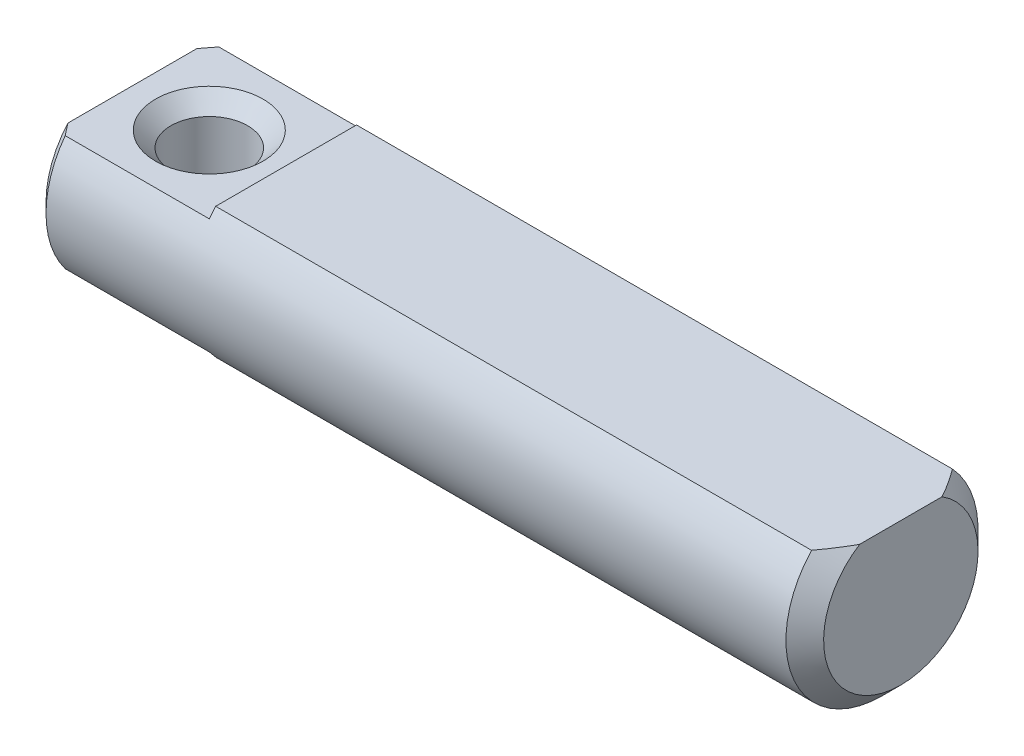
SolidWorks part; units mm, degrees
ref_plane "Front Plane" through (0, 0, 0) normal (0, 0, 1) x (1, 0, 0)
ref_plane "Top Plane" through (0, 0, 0) normal (0, 1, 0) x (1, 0, 0)
ref_plane "Right Plane" through (0, 0, 0) normal (1, 0, 0) x (0, 0, -1)
ref_plane "Plane1" through (0, 0, 0) normal (0, 0, 1) x (1, 0, 0)
sketch "Sketch1" plane through (0, 0, 0) normal (0, 0, 1) x (1, 0, 0)
  line L0 (0, 0) -> (0, 2.25)
  line L1 (0, 2.25) -> (0.25, 2.5)
  line L2 (0.25, 2.5) -> (19.5095, 2.5)
  line L3 (19.5095, 2.5) -> (20, 2.0095)
  line L4 (20, 2.0095) -> (20, 0)
  line L5 (20, 0) -> (0, 0)
  line L6 (20, 0) -> (0, 0) construction
revolve "Revolve1" add sketch "Sketch1" angle 360 about L6
cosmetic thread "Cosmetic Thread1" parameters "D1"=15, "D2"=4.11
ref_plane "Plane2" through (0, 0, 0) normal (1, 0, 0) x (0, 0, -1)
sketch "Sketch2" plane through (0, 0, 0) normal (1, 0, 0) x (0, 0, -1)
  line L0 (-10, 1.5) -> (10, 1.5)
  line L1 (10, 1.5) -> (10, 4.5)
  line L2 (10, 4.5) -> (-10, 4.5)
  line L3 (-10, 4.5) -> (-10, 1.5)
extrude "Cut-Extrude1" cut sketch "Sketch2" along normal blind 4
ref_plane "Plane3" through (0, 0, 0) normal (1, 0, 0) x (0, 0, -1)
sketch "Sketch3" plane through (0, 0, 0) normal (1, 0, 0) x (0, 0, -1)
  line L0 (-10, -1.5) -> (-10, -4.5)
  line L1 (-10, -4.5) -> (10, -4.5)
  line L2 (10, -4.5) -> (10, -1.5)
  line L3 (10, -1.5) -> (-10, -1.5)
extrude "Cut-Extrude2" cut sketch "Sketch3" along normal blind 4
ref_plane "Plane4" through (0, 0, 0) normal (0, 0, 1) x (1, 0, 0)
sketch "Sketch4" plane through (0, 0, 0) normal (0, 0, 1) x (1, 0, 0)
  line L0 (2, 1.5) -> (3.4, 1.5)
  line L1 (3.4, 1.5) -> (3, 1.1)
  line L2 (3, 1.1) -> (3, -1.1)
  line L3 (3, -1.1) -> (3.4, -1.5)
  line L4 (3.4, -1.5) -> (2, -1.5)
  line L5 (2, -1.5) -> (2, 1.5)
  line L6 (2, -1.5) -> (2, 1.5) construction
revolve "Cut-Revolve1" cut sketch "Sketch4" angle 360 about L6
sketch "Sketch5" plane through (0, 0, 0) normal (0, 0, 1) x (1, 0, 0)
  line L0 (19.5095, 2.5) -> (4, 2.5) construction
  line L1 (0, 2.5) -> (20, 2.5)
  line L2 (0, 2.5) -> (0, 1.7)
  line L3 (0, 1.7) -> (20, 1.7)
  line L4 (20, 2.5) -> (20, 1.7)
  line L5 (0, 1.5) -> (0, -1.5) construction
  line L6 (20, -2.0095) -> (20, 2.0095) construction
  dimension "D1" = 0.8
extrude "Cut-Extrude3" cut sketch "Sketch5" against normal through all and the other way through all
